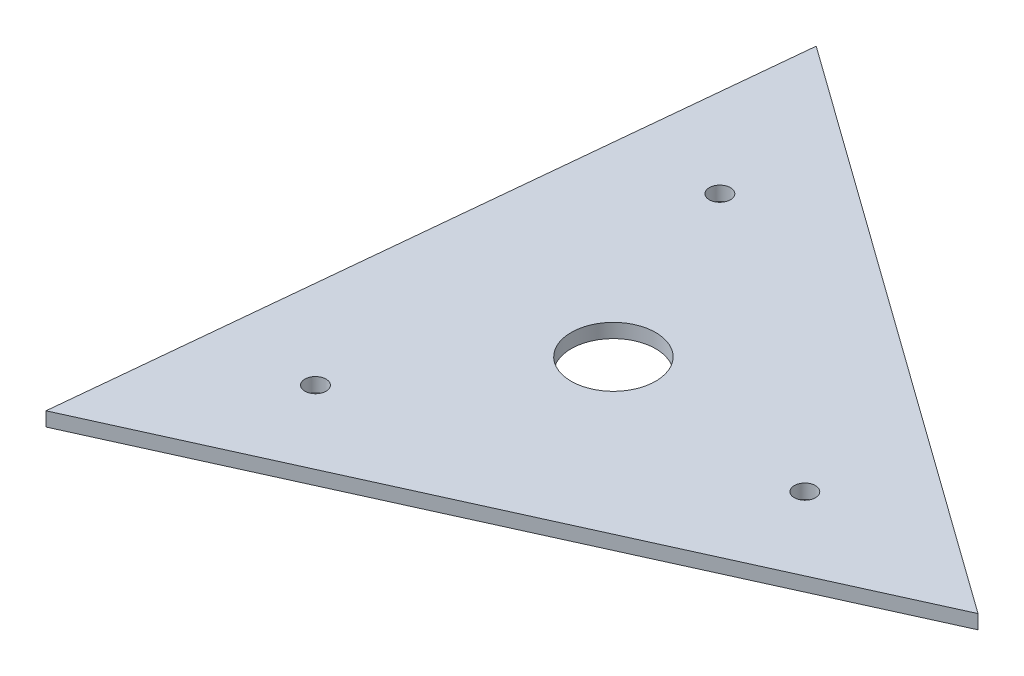
SolidWorks part; units mm, degrees
ref_plane "Front Plane" through (0, 0, 0) normal (0, 0, 1) x (1, 0, 0)
ref_plane "Top Plane" through (0, 0, 0) normal (0, 1, 0) x (1, 0, 0)
ref_plane "Right Plane" through (0, 0, 0) normal (1, 0, 0) x (0, 0, -1)
sketch "Sketch1" plane through (0, 0, 0) normal (0, 1, 0) x (1, 0, 0)
  line L0 (22.5, 163.1015) -> (-22.5, 163.1015) construction
  line L1 (287.2727, -28.421) -> (-119.023, 262.9959)
  line L2 (-119.023, 262.9959) -> (-168.2497, -234.5749)
  line L3 (-168.2497, -234.5749) -> (287.2727, -28.421)
  line L4 (-62.5, 138.1015) -> (-88.3494, -123.1773) construction
  line L5 (-88.3494, -123.1773) -> (150.8494, -14.9241) construction
  line L6 (150.8494, -14.9241) -> (-62.5, 138.1015) construction
  line L7 (152.5, -62.0652) -> (22.5, 163.1015) construction
  line L8 (-22.5, 163.1015) -> (-152.5, -62.0652) construction
  line L9 (-130, -101.0363) -> (130, -101.0363) construction
  line L10 (-152.5, -62.0652) -> (-130, -101.0363) construction
  line L11 (130, -101.0363) -> (152.5, -62.0652) construction
  line L12 (-22.5, 163.1015) -> (0, 202.0726) construction
  line L13 (0, 202.0726) -> (22.5, 163.1015) construction
  line L14 (152.5, -62.0652) -> (175, -101.0363) construction
  line L15 (175, -101.0363) -> (130, -101.0363) construction
  line L16 (-130, -101.0363) -> (-175, -101.0363) construction
  line L17 (-175, -101.0363) -> (-152.5, -62.0652) construction
  line L18 (-152.5, -62.0652) -> (-109.1987, -37.0652) construction
  line L19 (-130, -101.0363) -> (-86.6987, -76.0363) construction
  line L20 (-86.6987, -76.0363) -> (-109.1987, -37.0652) construction
  line L21 (-108.3494, -88.5363) -> (-93.3494, -114.5171) construction
  line L22 (-93.3494, -114.5171) -> (-88.3494, -123.1773) construction
  circle A0 centre (0, 0) radius 144.3376 construction
  circle A1 centre (0, 0) radius 75.7929 construction
  circle A2 centre (-62.5, 138.1015) radius 7.5
  circle A3 centre (150.8494, -14.9241) radius 7.5
  circle A4 centre (-88.3494, -123.1773) radius 7.5
  circle A5 centre (0, 0) radius 101.0363 construction
  circle A6 centre (0, 0) radius 30
  point P14 (175, -101.0363)
  point P15 (0, 202.0726)
  point P16 (-175, -101.0363)
  dimension "D3" = 15
  dimension "D8" = 60
  dimension "D1" = 500
  dimension "D2" = 350
  dimension "D4" = 45
  dimension "D5" = 50
  dimension "D6" = 30
  dimension "D7" = 10
extrude "Boss-Extrude1" add sketch "Sketch1" along normal blind 10
